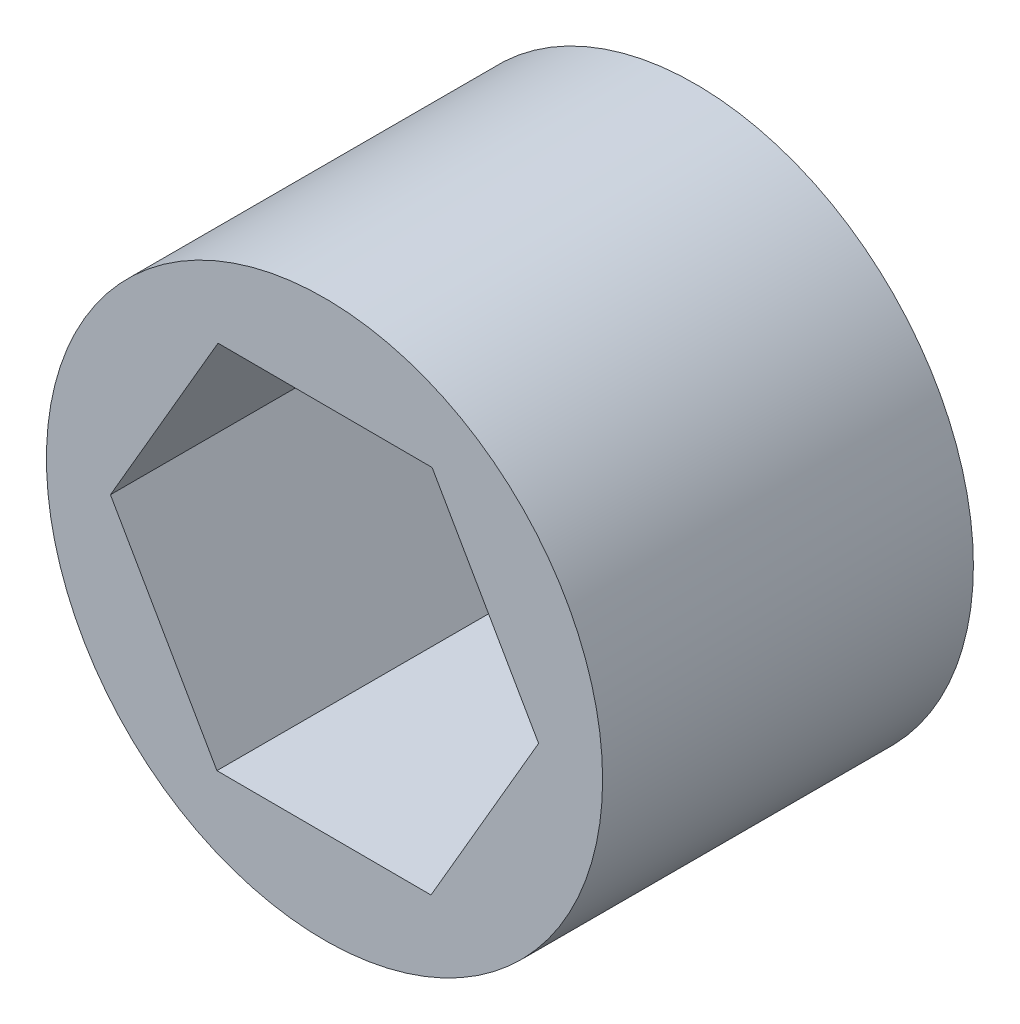
SolidWorks part; units mm, degrees
material "PET"
ref_plane "Front Plane" through (0, 0, 0) normal (0, 0, 1) x (1, 0, 0)
ref_plane "Top Plane" through (0, 0, 0) normal (0, 1, 0) x (1, 0, 0)
ref_plane "Right Plane" through (0, 0, 0) normal (1, 0, 0) x (0, 0, -1)
sketch "Sketch1" plane through (0, 0, 0) normal (0, 0, 1) x (1, 0, 0)
  line L1 (3.647, -6.361) -> (7.3323, -0.0221)
  line L2 (7.3323, -0.0221) -> (3.6853, 6.3389)
  line L3 (3.6853, 6.3389) -> (-3.647, 6.361)
  line L4 (-3.647, 6.361) -> (-7.3323, 0.0221)
  line L5 (-7.3323, 0.0221) -> (-3.6853, -6.3389)
  line L6 (-3.6853, -6.3389) -> (3.647, -6.361)
  circle A0 centre (0, 0) radius 9.525
  circle A1 centre (0, 0) radius 6.35 construction
  dimension "D1" = 19.05
  dimension "D2" = 12.7
extrude "Boss-Extrude1" add sketch "Sketch1" along normal blind 12.7
